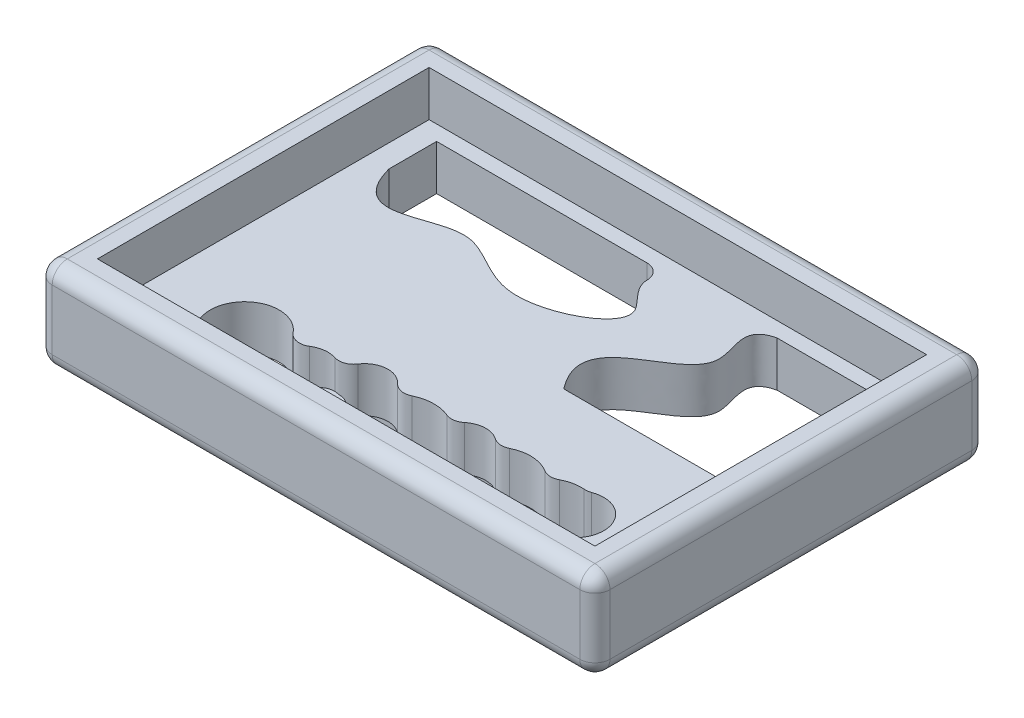
SolidWorks part; units mm, degrees
ref_plane "Front Plane" through (0, 0, 0) normal (0, 0, 1) x (1, 0, 0)
ref_plane "Top Plane" through (0, 0, 0) normal (0, 1, 0) x (1, 0, 0)
ref_plane "Right Plane" through (0, 0, 0) normal (1, 0, 0) x (0, 0, -1)
sketch "Sketch1" plane through (0, 0, 0) normal (0, 1, 0) x (1, 0, 0)
  line L0 (-46.99, 33.02) -> (46.99, 33.02)
  line L1 (-41.91, -27.94) -> (41.91, -27.94)
  line L2 (-41.91, -27.94) -> (-41.91, 27.94)
  line L3 (-41.91, 27.94) -> (41.91, 27.94)
  line L4 (41.91, -27.94) -> (41.91, 27.94)
  line L5 (0, 27.94) -> (0, -27.94) construction
  line L6 (-41.91, 0) -> (41.91, 0) construction
  line L7 (46.99, -33.02) -> (46.99, 33.02)
  line L8 (-46.99, -33.02) -> (46.99, -33.02)
  line L9 (-46.99, -33.02) -> (-46.99, 33.02)
  point P0 (0, 0)
  dimension "D1" = 83.82
  dimension "D2" = 55.88
  dimension "D3" = 5.08
extrude "Boss-Extrude1" add sketch "Sketch1" along normal blind 15.24 contours L2 L1 L4 L3 | L0 L7 L8 L9
sketch "Sketch3" plane through (0, 0, 0) normal (0, 1, 0) x (1, 0, 0)
  line L1 (-41.91, -27.94) -> (41.91, -27.94)
  line L2 (-41.91, -27.94) -> (-41.91, 27.94)
  line L3 (-41.91, 27.94) -> (41.91, 27.94)
  line L4 (41.91, -27.94) -> (41.91, 27.94)
  line L5 (0, 27.94) -> (0, -27.94) construction
  line L6 (-41.91, 0) -> (41.91, 0) construction
  point P0 (0, 0)
extrude "Boss-Extrude2" add sketch "Sketch3" along normal blind 7.62
sketch "Sketch4" plane through (0, 0, 0) normal (0, -1, 0) x (1, 0, 0)
  line L0 (-30.48, 6.35) -> (30.48, 6.35) construction
  line L1 (-30.48, 7.62) -> (30.48, 7.62)
  line L2 (-30.48, 5.08) -> (30.48, 5.08)
  line L3 (-46.99, 33.02) -> (46.99, 33.02) construction
  line L4 (-46.99, -33.02) -> (-46.99, 33.02) construction
  arc A0 (-30.48, 7.62) -> (-30.48, 5.08) centre (-30.48, 6.35) ccw
  arc A1 (30.48, 5.08) -> (30.48, 7.62) centre (30.48, 6.35) ccw
  point P2 (0, 6.35)
  point P9 (-31.75, 6.35)
  point P10 (31.75, 6.35)
  dimension "D4" = 1.27
  dimension "D1" = 25.4
  dimension "D2" = 63.5
  dimension "D3" = 46.99
extrude "Boss-Extrude3" add sketch "Sketch4" along normal blind 10
fillet "Fillet1" radius 2.54 12 edges at (-46.99, 15.24, 0) (-46.99, 0, 0) (0, 15.24, -33.02) (-46.99, 7.62, -33.02) (0, 0, -33.02) (46.99, 15.24, 0) (46.99, 7.62, -33.02) (46.99, 0, 0) (-46.99, 7.62, 33.02) (0, 15.24, 33.02) (46.99, 7.62, 33.02) (0, 0, 33.02)
sketch "Sketch5" plane through (0, 0, 0) normal (0, -1, 0) x (1, 0, 0)
  line L0 (44.45, -33.02) -> (-44.45, -33.02) construction
  line L1 (-38.1, 0) -> (38.1, 0)
  line L2 (-38.1, 0) -> (-38.1, -25.4)
  line L3 (-38.1, -25.4) -> (38.1, -25.4)
  line L4 (38.1, 0) -> (38.1, -25.4)
  line L5 (-38.1, -17.338) -> (-38.1, -25.4)
  line L6 (-2.6661, -25.4) -> (-38.1, -25.4)
  line L7 (19.2872, -25.4) -> (38.1, -25.4)
  line L8 (38.1, 0) -> (8.7203, 0)
  arc A0 (-26.1411, 24.0344) -> (-22.2422, 14.6317) centre (-26.7764, 18.2613) ccw
  arc A1 (-18.9046, 15.193) -> (-15.1406, 14.7201) centre (-16.5172, 18.9794) ccw
  arc A3 (-12.239, 13.7015) -> (-6.0438, 13.2309) centre (-8.9592, 15.8641) ccw
  arc A4 (-3.0509, 13.814) -> (2.682, 13.6481) centre (0, 20.108) ccw
  arc A5 (12.8446, 13.2488) -> (19.0769, 13.5437) centre (15.6965, 18.9794) ccw
  arc A6 (5.275, 13.2593) -> (10.258, 13.0568) centre (7.8996, 16.4315) ccw
  arc A7 (21.6254, 13.6217) -> (25.0665, 12.9147) centre (24.5194, 18.9794) ccw
  arc A8 (26.1874, 12.7629) -> (30.4333, 21.5199) centre (27.9049, 17.338) ccw
  arc A10 (-20.8097, 23.5638) -> (-26.1411, 24.0344) centre (-23.8013, 20.108) ccw
  arc A11 (-12.5391, 21.0316) -> (-18.1951, 23.1294) centre (-16.5172, 18.9794) ccw
  arc A12 (-9.1499, 19.788) -> (-9.7624, 19.7097) centre (-8.9592, 15.8641) ccw
  arc A13 (6.6693, 22.2157) -> (-6.8027, 21.7344) centre (0, 20.108) ccw
  arc A15 (19.0769, 24.4151) -> (9.6333, 21.0316) centre (15.6965, 18.9794) ccw
  arc A16 (29.6199, 22.306) -> (21.6254, 24.3372) centre (24.5194, 18.9794) ccw
  arc A17 (8.6366, 20.4822) -> (6.6693, 22.2157) centre (9.0912, 22.9811) cw
  arc A18 (-6.8027, 21.7344) -> (-9.1499, 19.788) centre (-9.2731, 22.325) cw
  arc A19 (-3.0509, 13.814) -> (-6.0438, 13.2309) centre (-4.1589, 11.5283) ccw
  arc A20 (-18.1951, 23.1294) -> (-20.8097, 23.5638) centre (-19.1472, 25.4842) cw
  arc A21 (-9.7624, 19.7097) -> (-12.5391, 21.0316) centre (-10.2817, 22.196) cw
  arc A22 (-12.239, 13.7015) -> (-15.1406, 14.7201) centre (-14.3595, 12.3032) ccw
  arc A23 (-22.2422, 14.6317) -> (-18.9046, 15.193) centre (-20.2593, 13.0444) cw
  arc A24 (21.6254, 24.3372) -> (19.0769, 24.4151) centre (20.4183, 26.5721) cw
  arc A25 (21.6254, 13.6217) -> (19.0769, 13.5437) centre (20.4183, 11.3868) ccw
  arc A26 (5.275, 13.2593) -> (2.682, 13.6481) centre (3.6559, 11.3023) ccw
  arc A27 (12.8446, 13.2488) -> (10.258, 13.0568) centre (11.713, 10.9748) ccw
  arc A28 (30.4333, 21.5199) -> (29.6199, 22.306) centre (31.7474, 23.6936) cw
  arc A29 (26.1874, 12.7629) -> (25.0665, 12.9147) centre (25.2947, 10.3849) ccw
  arc A30 (-0.1269, -22.7967) -> (-2.6661, -25.4) centre (-2.6661, -22.86) cw
  spline S0 degree 3 poles (-38.1, -17.338) (-35.188, -6.8377) (-22.3961, -19.5472) (-11.0766, -5.4247) (8.0485, -15.4078) (0.3299, -20.2131) (-0.1319, -22.5949) (-0.1269, -22.7967) knots 0 0 0 0 0.327917 0.565866 0.827055 0.928649 0.941908 0.941908 0.941908 0.941908
  spline S1 degree 3 poles (8.7203, 0) (0.7179, -10.321) (24.6903, -11.2218) (14.3026, -24.2796) (19.2872, -25.4) knots 0 0 0 0 0.689244 1 1 1 1
  spline S2 degree 2 poles (8.6366, 20.4822) (9.3655, 20.3804) (9.6333, 21.0316) knots 0 0 0 1 1 1
  point P45 (6.9863, 20.4461)
  point P48 (-6.9396, 19.2338)
  point P55 (-12.1067, 18.215)
  point P62 (20.3286, 23.3974)
  point P71 (29.9218, 21.7892)
  dimension "D5" = 2.54
  dimension "D6" = 2.54
  dimension "D7" = 2.54
  dimension "D8" = 2.54
  dimension "D1" = 25.4
  dimension "D2" = 7.62
  dimension "D3" = 76.2
  dimension "D4" = 38.1
extrude "Cut-Extrude1" cut sketch "Sketch5" against normal through all contours S0 L2 L3 | L1 S1 L3 L4 | A6 A27 A5 A25 A7 A29 A8 A28 A16 A24 A15 S2 A17 A13 A18 A12 A21 A11 A20 A10 A0 A23 A1 A22 A3 A19 A4 A26
